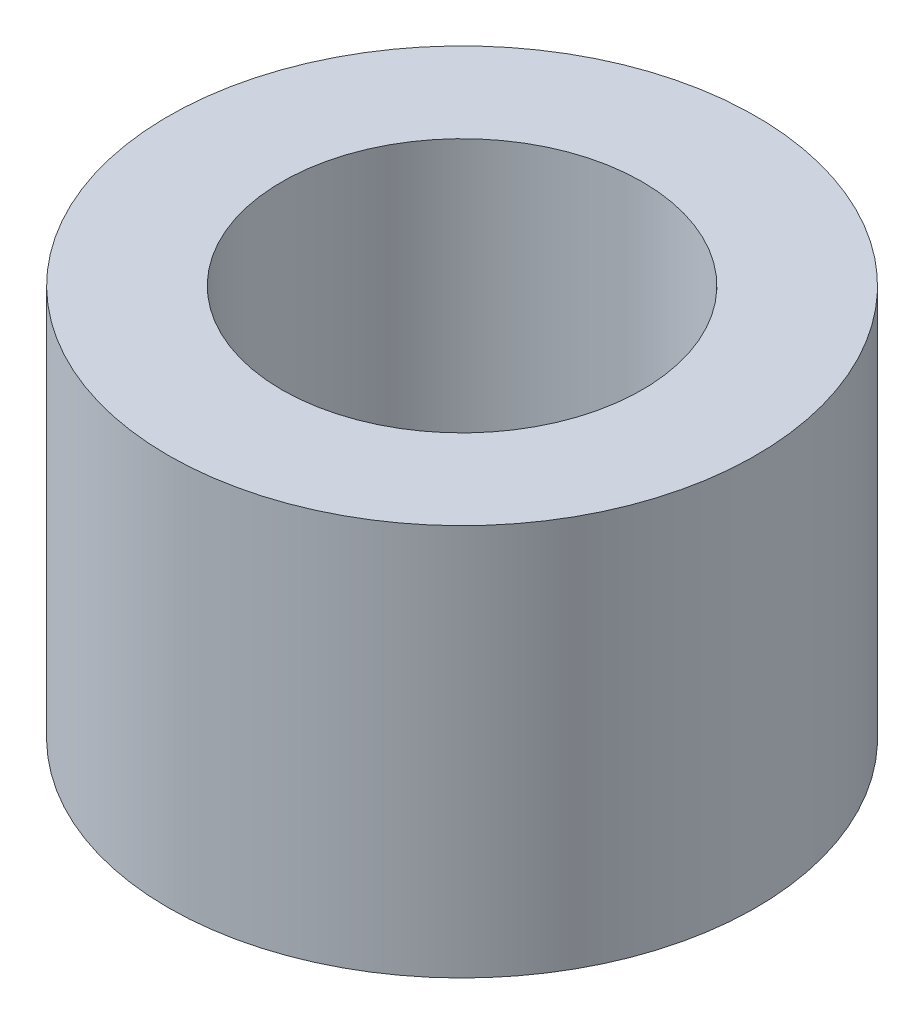
SolidWorks part; units mm, degrees
ref_plane "Front Plane" through (0, 0, 0) normal (0, 0, 1) x (1, 0, 0)
ref_plane "Top Plane" through (0, 0, 0) normal (0, 1, 0) x (1, 0, 0)
ref_plane "Right Plane" through (0, 0, 0) normal (1, 0, 0) x (0, 0, -1)
sketch "Sketch1" plane through (0, 0, 0) normal (0, 1, 0) x (1, 0, 0)
  circle A0 centre (0, 0) radius 2.3813
  circle A1 centre (0, 0) radius 1.4605
  dimension "D1" = 4.7625
  dimension "D2" = 2.921
extrude "Boss-Extrude1" add sketch "Sketch1" along normal blind 3.175
